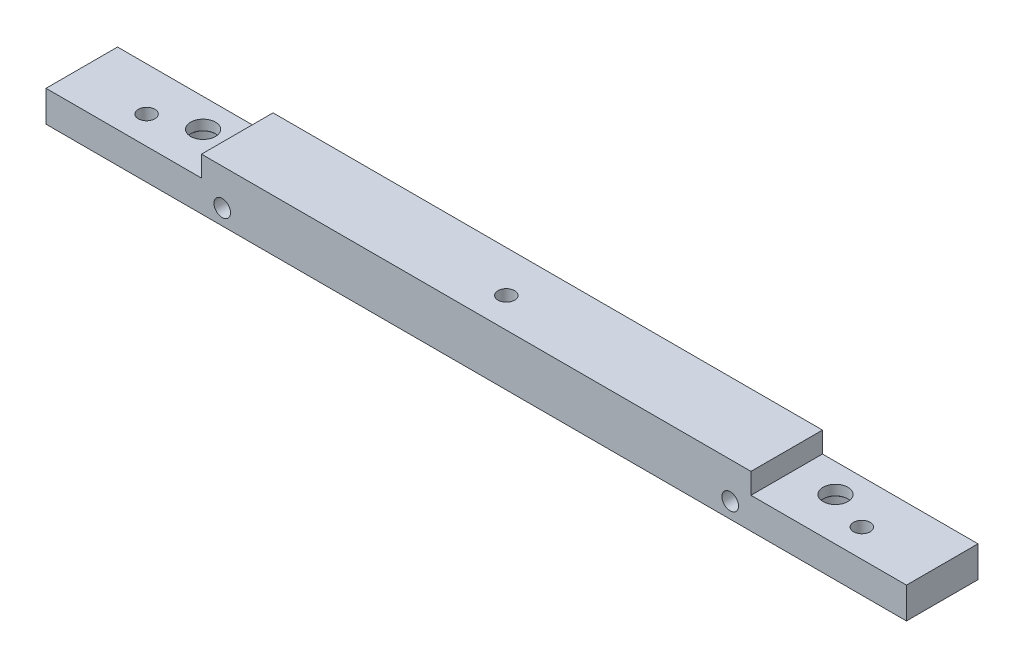
SolidWorks part; units mm, degrees
material "6061-T6 (SS)"
ref_plane "Front Plane" through (0, 0, 0) normal (0, 0, 1) x (1, 0, 0)
ref_plane "Top Plane" through (0, 0, 0) normal (0, 1, 0) x (1, 0, 0)
ref_plane "Right Plane" through (0, 0, 0) normal (1, 0, 0) x (0, 0, -1)
sketch "Sketch1" plane through (0, 0, 0) normal (0, 0, 1) x (1, 0, 0)
  line L0 (53, -3) -> (68, -3)
  line L1 (0, 0) -> (53, 0)
  line L2 (0, 0) -> (0, -3)
  line L4 (53, 0) -> (53, -3)
  line L5 (-15, -3) -> (0, -3)
  line L6 (-15, -3) -> (-15, -6)
  line L7 (-15, -6) -> (68, -6)
  line L8 (68, -3) -> (68, -6)
  dimension "D1" = 6
  dimension "D2" = 53
  dimension "D3" = 83
  dimension "D4" = 15
  dimension "D5" = 3
extrude "Boss-Extrude1" add sketch "Sketch1" along normal blind 8.5
hole_wizard "CBORE for M2 Socket Head Cap Screw1" positions "Sketch5" profile "Sketch4" counterbore size "M2" standard "JIS" end condition through all
sketch "Sketch5" plane through (0, -6, 0) normal (0, -1, 0) x (-1, 0, 0)
  line L0 (15, -8.5) -> (15, 0) construction
  line L1 (-68, -8.5) -> (-68, 0) construction
  line L2 (15, -8.5) -> (-68, -8.5) construction
  point P0 (4, -2.75)
  point P2 (-57, -2.75)
  dimension "D1" = 11
  dimension "D2" = 11
  dimension "D3" = 5.75
  dimension "D4" = 5.75
sketch "Sketch4" plane through (-4, -6, 2.75) normal (1, 0, 0) x (0, 0, -1)
  line L0 (0, 0) -> (0, 6)
  line L1 (0, 6) -> (1.2, 6)
  line L2 (1.2, 2.025) -> (1.2, 6)
  line L3 (1.2, 2.025) -> (1.225, 2)
  line L4 (1.225, 2) -> (2.2, 2)
  line L5 (2.2, 2) -> (2.2, 0)
  line L7 (0, 0) -> (2.2, 0)
  line L9 (-1.2, 2.025) -> (-1.225, 2) construction
  line L11 (0, -6.35) -> (0, 107.95) construction
  dimension "Thru Hole Dia." = 2.4
  dimension "Thru Hole Depth" = 6
  dimension "C'Bore Dia." = 4.4
  dimension "C'Bore Depth" = 2
  dimension "Mid C'Sink Dia." = 2.45
  dimension "Mid C'Sink Angle" = 90
sketch "Sketch8" plane through (0, 0, 8.5) normal (0, 0, 1) x (1, 0, 0)
  line L0 (53, 0) -> (0, 0) construction
  line L1 (0, 0) -> (53, 0)
  line L2 (0, 0) -> (0, -1)
  line L3 (0, -1) -> (53, -1)
  line L4 (53, 0) -> (53, -1)
  line L5 (53, -3) -> (53, 0) construction
  dimension "D1" = 53
  dimension "D2" = 1
extrude "Cut-Extrude1" cut sketch "Sketch8" against normal through all
hole_wizard "M2x0.4 Tapped Hole8" positions "Sketch10" profile "Sketch9" tap size "M2x0.4" standard "ANSI Metric" end condition through all
sketch "Sketch10" plane through (0, 0, 8.5) normal (0, 0, 1) x (1, 0, 0)
  line L0 (-15, -3) -> (-15, -6) construction
  line L2 (68, -6) -> (68, -3) construction
  line L3 (0, -1) -> (53, -1) construction
  point P0 (2, -4.5)
  point P2 (51, -4.5)
  dimension "D2" = 17
  dimension "D3" = 17
  dimension "D4" = 3.5
cosmetic thread "Hole Thread5" parameters "D2"=2
cosmetic thread "Hole Thread6" parameters "D2"=2
sketch "Sketch9" plane through (2, -4.5, 8.5) normal (1, 0, 0) x (0, -1, 0)
  line L0 (0, 0) -> (0, 8.5)
  line L1 (0, 8.5) -> (0.8, 8.5)
  line L2 (0.8, 8.5) -> (0.8, 0)
  line L5 (0.8, 0) -> (0, 0)
  line L11 (0, -6.35) -> (0, 107.95) construction
  dimension "Thru Tap Drill Dia." = 1.6
  dimension "Thru Tap Drill Depth" = 8.5
sketch "Sketch14" plane through (0, -6, 0) normal (0, -1, 0) x (1, 0, 0)
  line L0 (-15, 8.5) -> (-15, 0) construction
  line L1 (68, 8.5) -> (-15, 8.5)
  line L2 (68, 8.5) -> (68, 6.9)
  line L3 (68, 6.9) -> (-15, 6.9)
  line L4 (-15, 8.5) -> (-15, 6.9)
  dimension "D1" = 1.6
extrude "Cut-Extrude2" cut sketch "Sketch14" against normal blind 10
sketch "Sketch15" plane through (0, -6, 0) normal (0, -1, 0) x (1, 0, 0)
  line L1 (-15, 6.9) -> (-8, 6.9)
  line L2 (-15, 6.9) -> (-15, 4.2)
  line L3 (-15, 4.2) -> (-8, 4.2)
  line L4 (-8, 6.9) -> (-8, 4.2)
  line L5 (68, 6.9) -> (61, 6.9)
  line L6 (68, 6.9) -> (68, 4.2)
  line L7 (68, 4.2) -> (61, 4.2)
  line L8 (61, 6.9) -> (61, 4.2)
  dimension "D1" = 7
  dimension "D2" = 7
  dimension "D3" = 2.7
  dimension "D4" = 2.7
hole_wizard "M2x0.4 Tapped Hole7" positions "Sketch17" profile "Sketch18" tap size "M2x0.4" standard "JIS" end condition through all
sketch "Sketch17" plane through (0, -6, 0) normal (0, -1, 0) x (-1, 0, 0)
  point P0 (8, -4.2)
  point P3 (-61, -4.2)
sketch "Sketch18" plane through (-8, -6, 4.2) normal (1, 0, 0) x (0, 0, -1)
  line L0 (0, 0) -> (0, 5)
  line L1 (0, 5) -> (0.8, 5)
  line L2 (0.8, 5) -> (0.8, 0)
  line L5 (0.8, 0) -> (0, 0)
  line L11 (0, -6.35) -> (0, 107.95) construction
  dimension "Thru Tap Drill Dia." = 1.6
  dimension "Thru Tap Drill Depth" = 5
cosmetic thread "Hole Thread8" parameters "D2"=2
cosmetic thread "Hole Thread9" parameters "D2"=2
sketch "Sketch19" plane through (0, -6, 0) normal (0, -1, 0) x (1, 0, 0)
  line L0 (-15, 0) -> (68, 0) construction
  line L1 (-15, 6.9) -> (-15, 0) construction
  point P0 (26.5, 4)
  dimension "D1" = 4
  dimension "D2" = 41.5
hole_wizard "M2x0.4 Tapped Hole6" positions "Sketch21" profile "Sketch20" tap size "M2x0.4" standard "ANSI Metric"
sketch "Sketch21" plane through (0, -6, 0) normal (0, -1, 0) x (-1, 0, 0)
  point P0 (-26.5, -4)
sketch "Sketch20" plane through (26.5, -6, 4) normal (1, 0, 0) x (0, 0, -1)
  line L0 (0, 0) -> (0, 5.6807)
  line L1 (0, 5.6807) -> (0.8, 5.2)
  line L2 (0.8, 5.2) -> (0.8, 0)
  line L5 (0.8, 0) -> (0, 0)
  line L10 (0, 5.6807) -> (-0.8, 5.2) construction
  line L11 (0, -6.35) -> (0, 107.95) construction
  dimension "Tap Drill Dia." = 1.6
  dimension "Tap Drill Depth" = 5.2
  dimension "Drill Angle" = 118
cosmetic thread "Hole Thread10" parameters "D1"=4, "D2"=2
